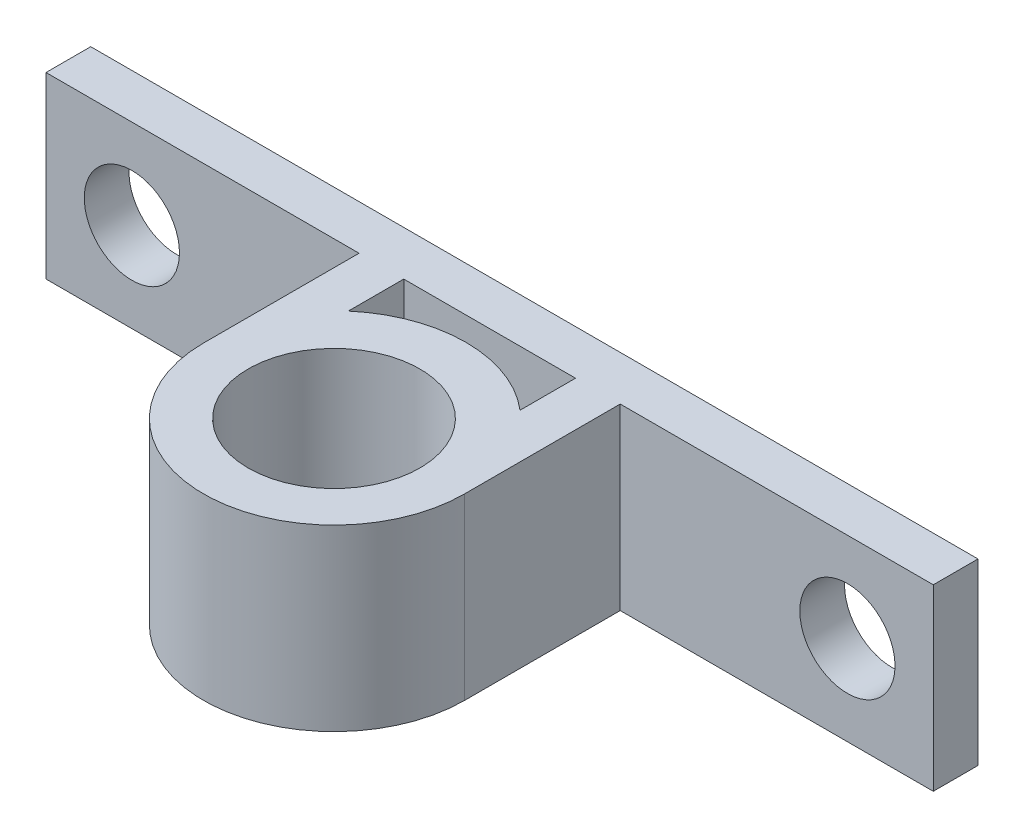
SolidWorks part; units mm, degrees
ref_plane "Front Plane" through (0, 0, 0) normal (0, 0, 1) x (1, 0, 0)
ref_plane "Top Plane" through (0, 0, 0) normal (0, 1, 0) x (1, 0, 0)
ref_plane "Right Plane" through (0, 0, 0) normal (1, 0, 0) x (0, 0, -1)
sketch "Sketch1" plane through (0, 0, 0) normal (0, 1, 0) x (1, 0, 0)
  line L0 (0, 0) -> (14.2506, 0) construction
  line L1 (0, 0) -> (0, 17.6258) construction
  line L3 (-6.096, 0) -> (-6.096, 14.224) construction
  line L4 (-9.271, 0) -> (-9.271, 11.049)
  line L5 (-9.271, 11.049) -> (-31.496, 11.049)
  line L6 (-6.096, 14.224) -> (-31.496, 14.224)
  line L7 (-31.496, 11.049) -> (-31.496, 14.224)
  line L9 (-6.096, 14.224) -> (6.096, 14.224)
  line L11 (9.271, 0) -> (9.271, 11.049)
  line L12 (31.496, 11.049) -> (31.496, 14.224)
  line L13 (6.096, 14.224) -> (31.496, 14.224)
  line L14 (9.271, 11.049) -> (31.496, 11.049)
  line L17 (-6.096, 7.112) -> (-6.096, 11.049)
  line L18 (6.096, 7.112) -> (6.096, 11.049)
  line L19 (-6.096, 11.049) -> (6.096, 11.049)
  circle A0 centre (0, 0) radius 6.096
  circle A1 centre (0, 0) radius 9.271 construction
  arc A3 (9.271, 0) -> (-9.271, 0) centre (0, 0) cw
  arc A5 (-6.096, 7.112) -> (6.096, 7.112) centre (0, 0) cw
  point P18 (0, 14.224)
  point P19 (0, 10.668)
  dimension "D1" = 12.192
  dimension "D2" = 3.175
  dimension "D3" = 14.224
  dimension "D4" = 3.175
  dimension "D5" = 25.4
  dimension "D6" = 12.192
extrude "Boss-Extrude1" add sketch "Sketch1" along normal blind 12.7
sketch "Sketch2" plane through (0, 0, -11.049) normal (0, 0, 1) x (1, 0, 0)
  line L0 (-31.496, 6.35) -> (-9.271, 6.35) construction
  line L1 (-31.496, 12.7) -> (-31.496, 0) construction
  line L2 (-9.271, 12.7) -> (-9.271, 0) construction
  line L6 (0, 0) -> (0, 12.7) construction
  line L7 (9.271, 12.7) -> (-9.271, 12.7) construction
  circle A0 centre (-25.4, 6.35) radius 3.3782
  circle A1 centre (25.4, 6.35) radius 3.3782
  dimension "D1" = 6.7564
  dimension "D2" = 25.4
extrude "Cut-Extrude1" cut sketch "Sketch2" against normal through all
